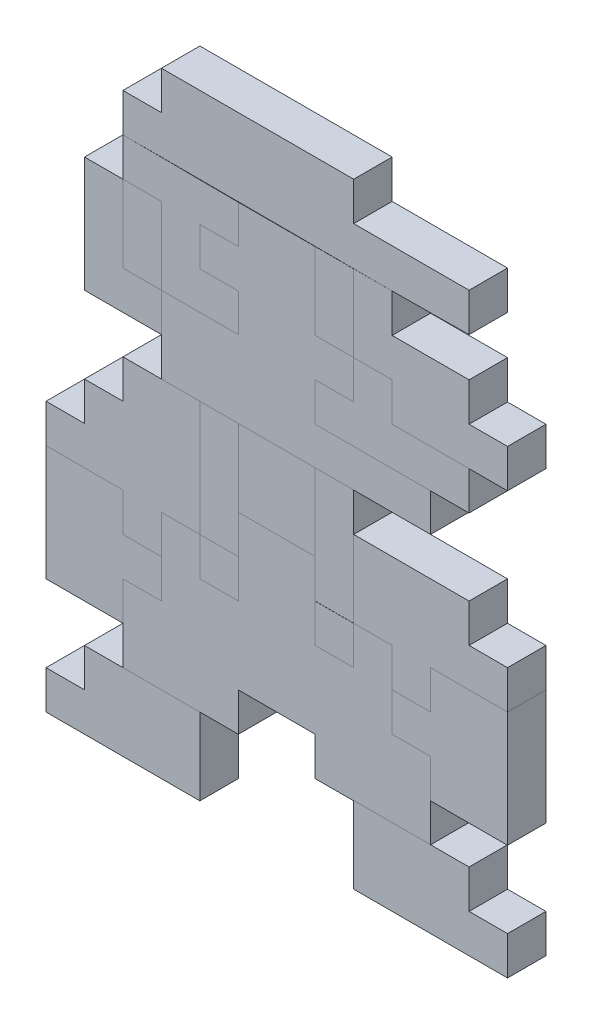
SolidWorks part; units mm, degrees
ref_plane "Front Plane" through (0, 0, 0) normal (0, 0, 1) x (1, 0, 0)
ref_plane "Top Plane" through (0, 0, 0) normal (0, 1, 0) x (1, 0, 0)
ref_plane "Right Plane" through (0, 0, 0) normal (1, 0, 0) x (0, 0, -1)
sketch "Sketch1" plane through (0, 0, 0) normal (0, 0, 1) x (1, 0, 0)
  line L0 (0, 0) -> (0, 50.8)
  line L1 (0, 50.8) -> (-25.4, 50.8)
  line L2 (-25.4, 50.8) -> (-25.4, 0)
  line L3 (-25.4, 0) -> (0, 0)
extrude "Boss-Extrude1" add sketch "Sketch1" along normal blind 25.4
sketch "Sketch2" plane through (0, 0, 25.4) normal (0, 0, 1) x (1, 0, 0)
  line L0 (0, 0) -> (0, -25.4)
  line L1 (0, -25.4) -> (-25.4, -25.4)
  line L2 (-25.4, -25.4) -> (-25.4, -50.8)
  line L3 (-25.4, -50.8) -> (76.2, -50.8)
  line L4 (76.2, -50.8) -> (76.2, -25.4)
  line L5 (76.2, -25.4) -> (25.4, -25.4)
  line L6 (25.4, -25.4) -> (25.4, 0)
  line L7 (25.4, 0) -> (0, 0)
extrude "Boss-Extrude2" add sketch "Sketch2" against normal blind 25.4 separate body
sketch "Sketch3" plane through (0, 0, 25.4) normal (0, 0, 1) x (1, 0, 0)
  line L0 (76.2, -25.4) -> (101.6, -25.4)
  line L1 (101.6, -25.4) -> (101.6, 0)
  line L2 (101.6, 0) -> (76.2, 0)
  line L3 (76.2, 0) -> (76.2, 25.4)
  line L4 (76.2, 25.4) -> (25.4, 25.4)
  line L5 (25.4, 25.4) -> (25.4, 50.8)
  line L6 (25.4, 50.8) -> (0, 50.8)
  line L7 (0, 0) -> (0, 50.8) construction
  line L8 (0, 50.8) -> (-25.4, 50.8) construction
  line L9 (0, 50.8) -> (0, 0)
  line L10 (0, 0) -> (25.4, 0)
  line L11 (25.4, 0) -> (25.4, -25.4)
  line L12 (25.4, -25.4) -> (76.2, -25.4)
extrude "Boss-Extrude10" add sketch "Sketch3" against normal blind 25.4 separate body
sketch "Sketch6" plane through (0, 0, 25.4) normal (0, 0, 1) x (1, 0, 0)
  line L0 (-25.4, 50.8) -> (-76.2, 50.8)
  line L1 (-76.2, 50.8) -> (-76.2, 25.4)
  line L2 (-76.2, 25.4) -> (-101.6, 25.4)
  line L3 (-101.6, 25.4) -> (-101.6, 0)
  line L4 (-101.6, 0) -> (-76.2, 0)
  line L5 (-76.2, 0) -> (-76.2, -24.9426)
  line L6 (-76.2, -24.9426) -> (-127, -24.9426)
  line L7 (-127, -24.9426) -> (-127, -75.7426)
  line L8 (-127, -75.7426) -> (50.8, -75.7426)
  line L9 (50.8, -75.7426) -> (50.8, -50.8)
  line L10 (-25.4, -50.8) -> (76.2, -50.8) construction
  line L11 (50.8, -50.8) -> (-25.4, -50.8)
  line L12 (-25.4, -50.8) -> (-25.4, -25.4)
  line L13 (-25.4, -25.4) -> (0, -25.4)
  line L14 (0, -25.4) -> (0, 0)
  line L15 (0, 0) -> (-25.4, 0)
  line L16 (-25.4, 0) -> (-25.4, 50.8)
extrude "Boss-Extrude12" add sketch "Sketch6" against normal blind 25.4 separate body
sketch "Sketch7" plane through (0, 0, 25.4) normal (0, 0, 1) x (1, 0, 0)
  line L0 (-127, -24.9426) -> (-127, 25.8574)
  line L1 (-127, 25.8574) -> (-152.4, 25.8574)
  line L2 (-152.4, 25.8574) -> (-152.4, 51.2574)
  line L3 (-152.4, 51.2574) -> (-76.2, 50.8)
  line L4 (-76.2, 50.8) -> (-76.2, 25.4)
  line L5 (-76.2, 25.4) -> (-101.6, 25.4)
  line L6 (-101.6, 25.4) -> (-101.6, 0)
  line L7 (-101.6, 0) -> (-76.2, 0)
  line L8 (-76.2, 0) -> (-76.2, -24.9426)
  line L9 (-127, -24.9426) -> (-76.2, -24.9426)
extrude "Boss-Extrude13" add sketch "Sketch7" against normal blind 25.4 separate body
sketch "Sketch8" plane through (0, 0, 25.4) normal (0, 0, 1) x (1, 0, 0)
  line L1 (-127, 25.8574) -> (-152.4, 25.8574)
  line L2 (-127, 25.8574) -> (-127, -24.9426)
  line L3 (-127, -24.9426) -> (-152.4, -24.9426)
  line L4 (-152.4, 25.8574) -> (-152.4, -24.9426)
extrude "Boss-Extrude14" add sketch "Sketch8" against normal blind 25.4 separate body
sketch "Sketch9" plane through (0, 0, 25.4) normal (0, 0, 1) x (1, 0, 0)
  line L0 (-152.4, 25.8574) -> (-152.4, -24.9426)
  line L1 (-152.4, -24.9426) -> (-127, -24.9426)
  line L2 (-127, -24.9426) -> (-127, -50.3426)
  line L3 (-127, -24.9426) -> (-127, -75.7426) construction
  line L4 (-127, -50.3426) -> (-177.8, -50.3426)
  line L5 (-177.8, -50.3426) -> (-177.8, 25.8574)
  line L6 (-177.8, 25.8574) -> (-152.4, 25.8574)
extrude "Boss-Extrude15" add sketch "Sketch9" against normal blind 25.4 separate body
sketch "Sketch10" plane through (0, 0, 25.4) normal (0, 0, 1) x (1, 0, 0)
  line L0 (-152.4, 51.2574) -> (-152.4, 76.6574)
  line L1 (-152.4, 76.6574) -> (-127, 76.6574)
  line L2 (-127, 76.6574) -> (-127, 102.0574)
  line L3 (-127, 102.0574) -> (-22.6548, 102.0574)
  line L4 (-152.4, 51.2574) -> (25.4, 50.8)
  line L5 (76.2, 51.2574) -> (76.2, 76.6574)
  line L6 (76.2, 76.6574) -> (0, 76.6574)
  line L7 (0, 76.6574) -> (0, 102.0574)
  line L8 (0, 102.0574) -> (-22.6548, 102.0574)
  line L9 (25.4, 50.8) -> (76.2, 51.2574)
extrude "Boss-Extrude16" add sketch "Sketch10" against normal blind 25.4 separate body
sketch "Sketch11" plane through (0, 0, 25.4) normal (0, 0, 1) x (1, 0, 0)
  line L0 (50.8, -75.7426) -> (-25.4, -75.7426)
  line L1 (-127, -75.7426) -> (50.8, -75.7426) construction
  line L2 (-25.4, -75.7426) -> (-25.4, -126.5426)
  line L3 (-25.4, -126.5426) -> (-76.2, -126.5426)
  line L4 (-76.2, -126.5426) -> (-76.2, -75.7426)
  line L5 (-76.2, -75.7426) -> (-25.4, -75.7426)
  line L6 (-76.2, -75.7426) -> (-101.6, -75.7426)
  line L7 (-101.6, -75.7426) -> (-101.6, -151.9426)
  line L8 (-101.6, -151.9426) -> (-127, -151.9426)
  line L9 (-127, -151.9426) -> (-127, -177.3426)
  line L10 (-127, -177.3426) -> (-152.4, -177.3426)
  line L11 (-152.4, -177.3426) -> (-152.4, -151.9426)
  line L12 (-152.4, -151.9426) -> (-203.2, -151.9426)
  line L13 (-203.2, -151.9426) -> (-203.2, -126.5426)
  line L14 (-203.2, -126.5426) -> (-177.8, -126.5426)
  line L15 (-177.8, -126.5426) -> (-177.8, -101.1426)
  line L16 (-177.8, -101.1426) -> (-152.4, -101.1426)
  line L17 (-152.4, -101.1426) -> (-152.4, -75.7426)
  line L18 (-152.4, -75.7426) -> (-127, -75.7426)
  line L19 (-127, -75.7426) -> (-101.6, -75.7426)
  line M10 (-127, -75.7426) -> (50.8, -75.7426)
extrude "Boss-Extrude17" add sketch "Sketch11" against normal blind 25.4 separate body contours L4 L3 L2 M10 | L18 L17 L16 L15 L14 L13 L12 L11 L10 L9 L8 L7 M10
sketch "Sketch12" plane through (0, 0, 25.4) normal (0, 0, 1) x (1, 0, 0)
  line L0 (-25.4, -75.7426) -> (-25.4, -126.5426)
  line L1 (-25.4, -75.7426) -> (-25.4, -126.5426) construction
  line L2 (-25.4, -126.5426) -> (-76.2, -126.5426) construction
  line L3 (-25.4, -126.5426) -> (-76.2, -126.5426)
  line L4 (-76.2, -126.5426) -> (-76.2, -75.7426)
  line L5 (-76.2, -75.7426) -> (-101.6, -75.7426)
  line L6 (-101.6, -75.7426) -> (-101.6, -151.9426)
  line L7 (-76.2, -177.3426) -> (-25.4, -177.4198)
  line L8 (-101.6, -151.9426) -> (-76.2, -151.9426)
  line L9 (-101.6, -151.9426) -> (-101.6, -177.3426)
  line L10 (-101.6, -177.3426) -> (-76.2, -177.3426)
  line L11 (-101.6, -151.9426) -> (-127, -151.9426)
  line L12 (-127, -151.9426) -> (-127, -202.7426)
  line L13 (-127, -202.7426) -> (-152.4, -202.7426)
  line L14 (-152.4, -202.7426) -> (-152.4, -253.5426)
  line L15 (-152.4, -253.5426) -> (-76.2, -253.5426)
  line L16 (-76.2, -253.5426) -> (-76.2, -228.1426)
  line L17 (-76.2, -228.1426) -> (-25.4, -228.1426)
  line L18 (-25.4, -228.1426) -> (-25.4, -253.5426)
  line L19 (-25.4, -253.5426) -> (50.8, -253.5426)
  line L20 (50.8, -253.5426) -> (50.8, -202.8198)
  line L21 (50.8, -202.8198) -> (25.4, -202.8198)
  line L22 (25.4, -202.8198) -> (25.4, -152.0198)
  line L23 (25.4, -152.0198) -> (0, -152.0198)
  line L24 (-76.2, -151.9426) -> (-76.2, -177.3426)
  line L25 (0, -152.0198) -> (-25.4, -152.0198)
  line L26 (0, -152.0198) -> (0, -177.4198)
  line L27 (0, -177.4198) -> (-25.4, -177.4198)
  line L28 (0, -75.7426) -> (0, -152.0198)
  line L29 (-127, -75.7426) -> (50.8, -75.7426) construction
  line L30 (0, -75.7426) -> (-25.4, -75.7426)
  line L31 (-25.4, -152.0198) -> (-25.4, -177.4198)
  line L33 (-101.6, -151.9426) -> (-76.2, -151.9426)
  line L34 (-101.6, -151.9426) -> (-101.6, -177.3426)
  line L35 (-101.6, -177.3426) -> (-76.2, -177.3426)
  line L36 (-76.2, -151.9426) -> (-76.2, -177.3426)
  line L37 (0, -152.0198) -> (-25.4, -152.0198)
  line L38 (0, -152.0198) -> (0, -177.4198)
  line L39 (0, -177.4198) -> (-25.4, -177.4198)
  line L40 (-25.4, -152.0198) -> (-25.4, -177.4198)
sketch "Sketch13" plane through (0, 0, 25.4) normal (0, 0, 1) x (1, 0, 0)
  line L0 (-152.4, -177.3426) -> (-127, -177.3426)
  line L1 (-127, -177.3426) -> (-127, -202.7426)
  line L4 (-152.4, -177.3426) -> (-152.4, -151.9426)
  line L5 (-127, -202.7426) -> (-152.4, -202.7426)
  line L6 (-152.4, -202.7426) -> (-152.4, -228.1426)
  line L8 (-152.4, -228.1426) -> (-203.2, -228.1426)
  line L9 (-203.2, -228.1426) -> (-203.2, -151.9426)
  line L10 (-203.2, -151.9426) -> (-152.4, -151.9426)
extrude "Boss-Extrude26" add sketch "Sketch13" against normal blind 25.4 separate body
sketch "Sketch23" plane through (0, 0, 25.4) normal (0, 0, 1) x (1, 0, 0)
  line L0 (-76.2, -75.7426) -> (-76.2, -151.9426)
  line L1 (-76.2, -151.9426) -> (-101.6, -151.9426)
  line L2 (-101.6, -151.9426) -> (-101.6, -75.7426)
  line L3 (-101.6, -75.7426) -> (-76.2, -75.7426)
  line L4 (-25.4, -75.7426) -> (0, -75.7426)
  line L5 (0, -75.7426) -> (0, -151.9426)
  line L7 (0, -151.9426) -> (-25.4, -151.9426)
  line L8 (-25.4, -151.9426) -> (-25.4, -75.7426)
extrude "Boss-Extrude35" add sketch "Sketch23" against normal blind 25.4 separate body
extrude "Boss-Extrude36" add sketch "Sketch12" against normal blind 25.4 separate body contours L24 L8 L9 L10 | L25 L31 L27 L26
sketch "Sketch24" plane through (0, 0, 25.4) normal (0, 0, 1) x (1, 0, 0)
  line L0 (-25.4, -126.5426) -> (-76.2, -126.5426)
  line L1 (-76.2, -126.5426) -> (-76.2, -177.3426)
  line L2 (-76.2, -177.3426) -> (-101.6, -177.3426)
  line L3 (-101.6, -177.3426) -> (-101.6, -151.9426)
  line L4 (-101.6, -151.9426) -> (-127, -151.9426) construction
  line L5 (-101.6, -151.9426) -> (-101.6, -177.3426) construction
  line L6 (-101.6, -151.9426) -> (-127, -151.9426)
  line L7 (-127, -151.9426) -> (-127, -202.7426)
  line L8 (-127, -202.7426) -> (-152.4, -202.7426)
  line L9 (-152.4, -202.7426) -> (-152.4, -253.5426)
  line L10 (-152.4, -253.5426) -> (-76.2, -253.5426)
  line L11 (-76.2, -253.5426) -> (-76.2, -228.1426)
  line L12 (-76.2, -228.1426) -> (-25.4, -228.1426)
  line L14 (-25.4, -253.5426) -> (-25.4, -228.1426)
  line L15 (50.8, -253.5426) -> (-25.4, -253.5426)
  line L16 (50.8, -202.7426) -> (50.8, -253.5426)
  line L17 (25.4, -202.7426) -> (50.8, -202.7426)
  line L18 (25.4, -151.9426) -> (25.4, -202.7426)
  line L19 (0, -151.9426) -> (25.4, -151.9426)
  line L20 (0, -177.3426) -> (0, -151.9426)
  line L21 (-25.4, -177.3426) -> (0, -177.3426)
  line L22 (-25.4, -126.5426) -> (-25.4, -177.3426)
extrude "Boss-Extrude37" add sketch "Sketch24" against normal blind 25.4 separate body
sketch "Sketch25" plane through (0, 0, 25.4) normal (0, 0, 1) x (1, 0, 0)
  line L0 (-152.4, -253.5426) -> (-177.8, -253.5426)
  line L1 (-177.8, -253.5426) -> (-177.8, -278.9426)
  line L2 (-177.8, -278.9426) -> (-203.2, -278.9426)
  line L3 (-203.2, -278.9426) -> (-203.2, -304.3426)
  line L4 (-203.2, -304.3426) -> (-101.6, -304.3426)
  line L5 (-101.6, -304.3426) -> (-101.6, -253.5426)
  line L6 (-152.4, -253.5426) -> (-76.2, -253.5426) construction
  line L7 (-101.6, -253.5426) -> (-152.4, -253.5426)
extrude "Boss-Extrude38" add sketch "Sketch25" against normal blind 25.4 separate body
sketch "Sketch26" plane through (0, 0, 25.4) normal (0, 0, 1) x (1, 0, 0)
  line L0 (50.8, -253.2684) -> (76.2, -253.2684)
  line L1 (50.8, -253.5426) -> (50.8, -202.7426) construction
  line L2 (76.2, -253.2684) -> (76.2, -278.6684)
  line L3 (76.2, -278.6684) -> (101.6, -278.6684)
  line L4 (101.6, -278.6684) -> (101.6, -304.0684)
  line L5 (101.6, -304.0684) -> (0, -304.0684)
  line L6 (0, -304.0684) -> (0, -253.2684)
  line L7 (0, -253.2684) -> (50.8, -253.2684)
extrude "Boss-Extrude39" add sketch "Sketch26" against normal blind 25.4 separate body
sketch "Sketch27" plane through (0, 0, 25.4) normal (0, 0, 1) x (1, 0, 0)
  line L0 (25.4, -151.9426) -> (0, -151.9426)
  line L1 (0, -151.9426) -> (0, -101.1426)
  line L2 (0, -151.9426) -> (0, -75.7426) construction
  line L3 (0, -101.1426) -> (76.2, -101.1426)
  line L4 (76.2, -101.1426) -> (76.2, -126.5426)
  line L5 (76.2, -126.5426) -> (101.6, -126.5426)
  line L6 (101.6, -126.5426) -> (101.6, -151.9426)
  line L7 (101.6, -151.9426) -> (50.8, -151.9426)
  line L8 (50.8, -151.9426) -> (50.8, -177.3426)
  line L9 (50.8, -177.3426) -> (25.4, -177.3426)
  line L10 (25.4, -177.3426) -> (25.4, -151.9426)
extrude "Boss-Extrude40" add sketch "Sketch27" against normal blind 25.4 separate body
sketch "Sketch28" plane through (0, 0, 25.4) normal (0, 0, 1) x (1, 0, 0)
  line L0 (25.4, -177.3426) -> (50.8, -177.3426)
  line L1 (50.8, -177.3426) -> (50.8, -151.9426)
  line L2 (50.8, -151.9426) -> (101.6, -151.9426)
  line L3 (101.6, -151.9426) -> (101.6, -228.1426)
  line L4 (101.6, -228.1426) -> (50.8, -228.1426)
  line L5 (50.8, -228.1426) -> (50.8, -202.7426)
  line L6 (50.8, -253.5426) -> (50.8, -202.7426) construction
  line L7 (50.8, -202.7426) -> (25.4, -202.7426)
  line L8 (25.4, -202.7426) -> (25.4, -177.3426)
extrude "Boss-Extrude41" add sketch "Sketch28" against normal blind 25.4 separate body
